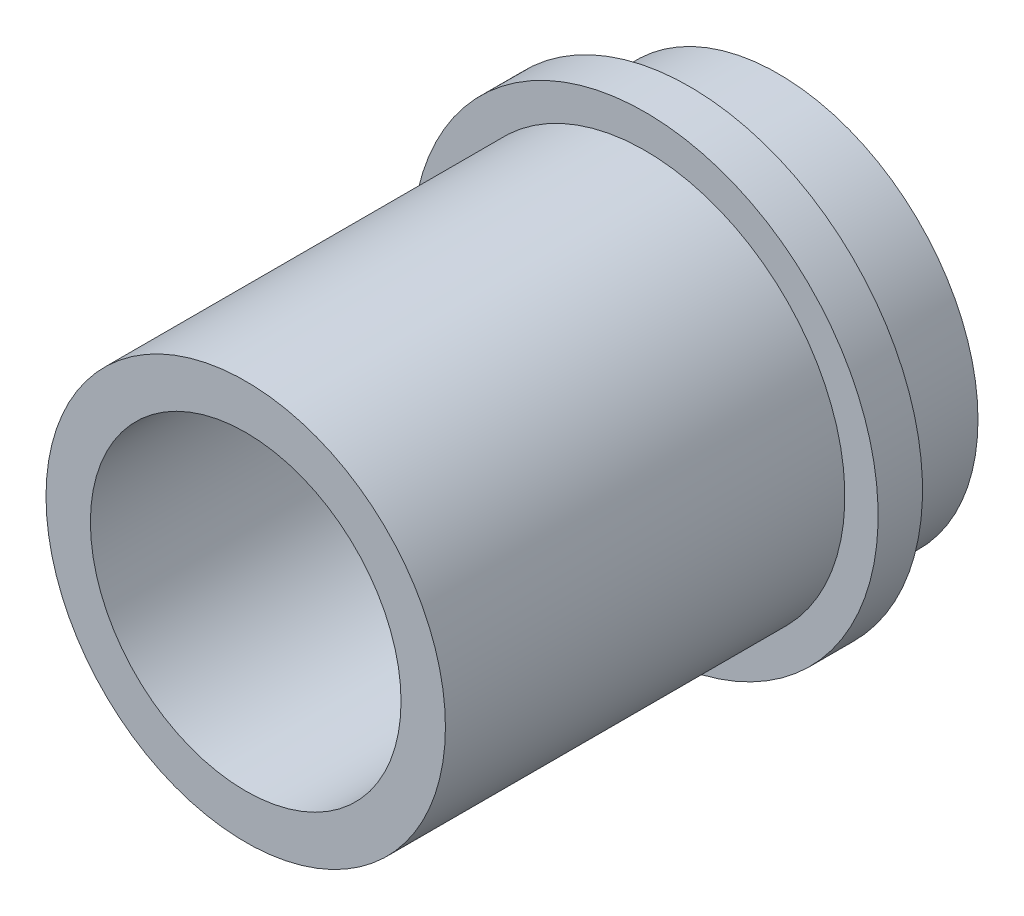
SolidWorks part; units mm, degrees
ref_plane "Front Plane" through (0, 0, 0) normal (0, 0, 1) x (1, 0, 0)
ref_plane "Top Plane" through (0, 0, 0) normal (0, 1, 0) x (1, 0, 0)
ref_plane "Right Plane" through (0, 0, 0) normal (1, 0, 0) x (0, 0, -1)
sketch "Sketch1" plane through (0, 0, 0) normal (0, 0, 1) x (1, 0, 0)
  circle A0 centre (0, 0) radius 4.5 construction
  circle A1 centre (0, 0) radius 4.5
  circle A2 centre (0, 0) radius 3.5 construction
  circle A3 centre (0, 0) radius 3.5
extrude "Boss-Extrude1" add sketch "Sketch1" along normal up to vertex (20 mm away) from vertex at 8
sketch "Sketch2" plane through (0, 0, 8) normal (0, 0, -1) x (-1, 0, 0)
  circle A0 centre (0, 0) radius 5.25
  circle A1 centre (0, 0) radius 3.5 construction
  circle A2 centre (0, 0) radius 3.5
  dimension "D1" = 10.5
extrude "Boss-Extrude2" add sketch "Sketch2" against normal up to vertex (3 mm away) from vertex at -2
